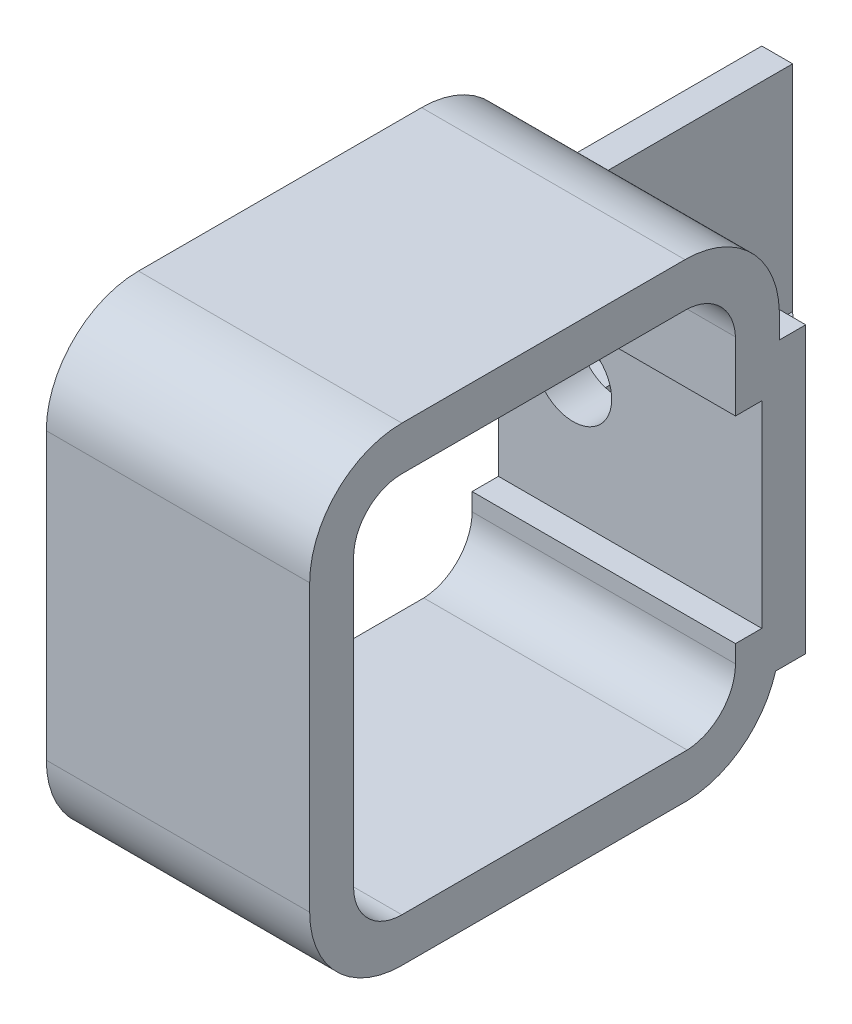
SolidWorks part; units mm, degrees
material "Custom Plastic"
ref_plane "Front Plane" through (0, 0, 0) normal (0, 0, 1) x (1, 0, 0)
ref_plane "Top Plane" through (0, 0, 0) normal (0, 1, 0) x (1, 0, 0)
ref_plane "Right Plane" through (0, 0, 0) normal (1, 0, 0) x (0, 0, -1)
sketch "Sketch1" plane through (0, 0, 0) normal (1, 0, 0) x (0, 0, -1)
  line L0 (-7.5376, 1.9693) -> (24.7124, 1.9693)
  line L1 (-13.0376, -3.5307) -> (-13.0376, -36.0307)
  line L2 (-7.5376, -41.5307) -> (24.9624, -41.5307)
  line L3 (30.4624, -3.5307) -> (30.4624, -11.3307)
  line L4 (30.4624, -11.3307) -> (33.4624, -11.3307)
  line L5 (33.4624, -11.3307) -> (33.4624, -33.7807)
  line L6 (33.4624, -33.7807) -> (30.4624, -33.7807)
  line L7 (30.4624, -33.7807) -> (30.4624, -35.7807)
  line L8 (-7.5376, 6.9693) -> (24.7124, 6.9693)
  line L9 (-18.0376, -3.5307) -> (-18.0376, -36.0307)
  line L10 (-7.5376, -46.5307) -> (25.0563, -46.5307)
  line L11 (35.0355, -38.7807) -> (35.0355, -38.7807)
  line L12 (38.4624, -38.7807) -> (35.0355, -38.7807)
  line L13 (38.4624, -6.3307) -> (38.4624, -38.7807)
  line L14 (35.4624, -6.3307) -> (38.4624, -6.3307)
  line L15 (35.4624, -3.5307) -> (35.4624, -6.3307)
  arc A0 (24.7124, 1.9693) -> (30.4624, -3.5307) centre (24.7124, -3.7864) cw
  arc A1 (30.4624, -35.7807) -> (24.9624, -41.5307) centre (24.7067, -35.7807) cw
  arc A2 (-7.5376, -41.5307) -> (-13.0376, -36.0307) centre (-7.5376, -36.0307) cw
  arc A3 (-13.0376, -3.5307) -> (-7.5376, 1.9693) centre (-7.5376, -3.5307) cw
  arc A4 (24.7124, 1.9693) -> (30.4624, -3.5307) centre (24.7124, -3.7864) cw
  arc A5 (-18.0376, -3.5307) -> (-7.5376, 6.9693) centre (-7.5376, -3.5307) cw
  arc A6 (-7.5376, -46.5307) -> (-18.0376, -36.0307) centre (-7.5376, -36.0307) cw
  arc A7 (35.0355, -38.7807) -> (25.0563, -46.5307) centre (24.7067, -35.7807) cw
  arc A8 (24.7124, -3.0307) -> (25.4673, -3.7529) centre (24.7124, -3.7864) cw
  arc A9 (24.7124, -3.0307) -> (25.4673, -3.7529) centre (24.7124, -3.7864) cw
  arc A10 (24.7124, 6.9693) -> (35.4624, -3.5307) centre (24.7124, -3.7837) cw
  dimension "D1" = 5
extrude "Boss-Extrude1" add sketch "Sketch1" along normal blind 30 contours A10 L8 A5 L9 A6 L10 A7 L12 L13 L14 L15 L1 A3 L0 A0 L3 L4 L5 L6 L7 A1 L2 A2
sketch "Sketch3" plane through (0, 0, -38.4624) normal (0, 0, -1) x (-1, 0, 0)
  line L2 (-8.5, -6.3307) -> (-8.5, -19.7307)
  line L3 (-17, -6.3307) -> (0, -6.3307)
  line L4 (-17, -6.3307) -> (-17, -38.7807)
  line L5 (-17, -38.7807) -> (0, -38.7807)
  line L6 (0, -6.3307) -> (0, -38.7807)
  circle A0 centre (-8.5, -19.7307) radius 4.4
  dimension "D2" = 8.8
  dimension "D3" = 13.4
extrude "Cut-Extrude1" cut sketch "Sketch3" against normal blind 30
sketch "Sketch4" plane through (0, 0, -38.4624) normal (0, 0, -1) x (-1, 0, 0)
  line L0 (-30, -38.7807) -> (0, -38.7807) construction
  line L1 (0, -6.3307) -> (-3.5114, -6.3307)
  line L2 (0, -6.3307) -> (0, -38.7807)
  line L3 (0, -38.7807) -> (-3.5114, -38.7807)
  line L4 (-3.5114, -6.3307) -> (-3.5114, -38.7807)
extrude "Boss-Extrude2" add sketch "Sketch4" along normal blind 25 contours L2 L1 L4 L3
sketch "Sketch5" plane through (3.5114, 0, 0) normal (1, 0, 0) x (0, 0, -1)
  circle A0 centre (53.4624, -22.6397) radius 3
  dimension "D1" = 6
extrude "Cut-Extrude2" cut sketch "Sketch5" against normal blind 20
sketch "Sketch6" plane through (0, 0, -38.4624) normal (0, 0, -1) x (-1, 0, 0)
  line L0 (-30, -6.3307) -> (-3.5114, -6.3307)
  line L1 (-3.5114, -6.3307) -> (-3.5114, -14.3307)
  line L2 (-3.5114, -6.3307) -> (-3.5114, -38.7807) construction
  line L3 (-3.5114, -14.3307) -> (-30, -14.3307)
  line L4 (-30, -6.3307) -> (-30, -38.7807) construction
  line L5 (-30, -14.3307) -> (-30, -6.3307)
  line L6 (-30, -38.7807) -> (-30, -30.7807)
  line L7 (-30, -30.7807) -> (-3.5114, -30.7807)
  line L8 (-3.5114, -30.7807) -> (-3.5114, -38.7807)
  line L9 (-3.5114, -38.7807) -> (-30, -38.7807)
  dimension "D1" = 8
  dimension "D2" = 8
  dimension "D3" = 26.4886
extrude "Boss-Extrude3" add sketch "Sketch6" along normal up to surface (25 mm away) contours L9 L6 L7 L8 up to face at (1.7557, -22.5557, -63.4624)
sketch "Sketch8" plane through (0, -30.7807, 0) normal (0, 1, 0) x (1, 0, 0)
  line L7 (3.5114, 63.4624) -> (30, 38.4624)
  line L8 (30, 38.4624) -> (30, 63.4624)
  line L9 (30, 63.4624) -> (3.5114, 63.4624)
extrude "Cut-Extrude5" cut sketch "Sketch8" against normal up to surface (8 mm away) contours L7 L8 L9 up to face at (15, -38.7807, -49.249)
sketch "Sketch9" plane through (3.5114, 0, 0) normal (1, 0, 0) x (0, 0, -1)
  line L0 (38.4624, -12.6135) -> (44.4624, -12.6135)
  line L1 (38.4624, -6.3307) -> (38.4624, -30.7807) construction
  line L2 (44.4624, -12.6135) -> (44.4624, -27.6135)
  line L3 (44.4624, -27.6135) -> (38.4624, -27.6135)
  line L4 (38.4624, -27.6135) -> (38.4624, -12.6135)
  line L5 (50.9624, -6.3307) -> (44.4624, -12.6135)
  line L7 (63.4624, -6.3307) -> (38.4624, -6.3307) construction
  line M6 (38.4624, -6.3307) -> (38.4624, -30.7807)
  dimension "D1" = 15
  dimension "D2" = 9.0401
  dimension "0.5mm" = 6
extrude "Cut-Extrude6" cut sketch "Sketch9" against normal up to surface (3.5114 mm away) contours L3 L2 L0 M6 up to face at (0, -22.6397, -56.4624)
